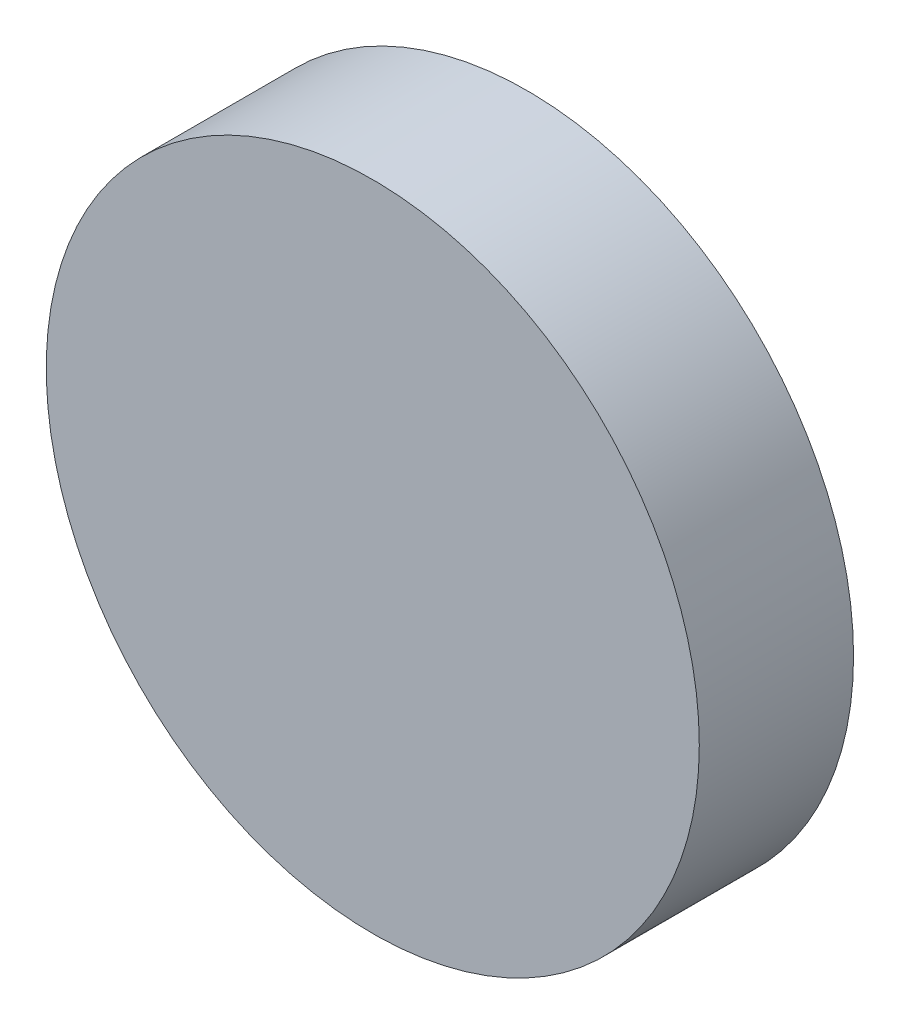
SolidWorks part; units mm, degrees
ref_plane "前视基准面" through (0, 0, 0) normal (0, 0, 1) x (1, 0, 0)
ref_plane "上视基准面" through (0, 0, 0) normal (0, 1, 0) x (1, 0, 0)
ref_plane "右视基准面" through (0, 0, 0) normal (1, 0, 0) x (0, 0, -1)
sketch "草图1" plane through (0, 0, 0) normal (0, 0, 1) x (1, 0, 0)
  circle A0 centre (0, 0) radius 6.35
  dimension "D1" = 12.7
extrude "凸台-拉伸1" add sketch "草图1" along normal blind 3 contours A0
